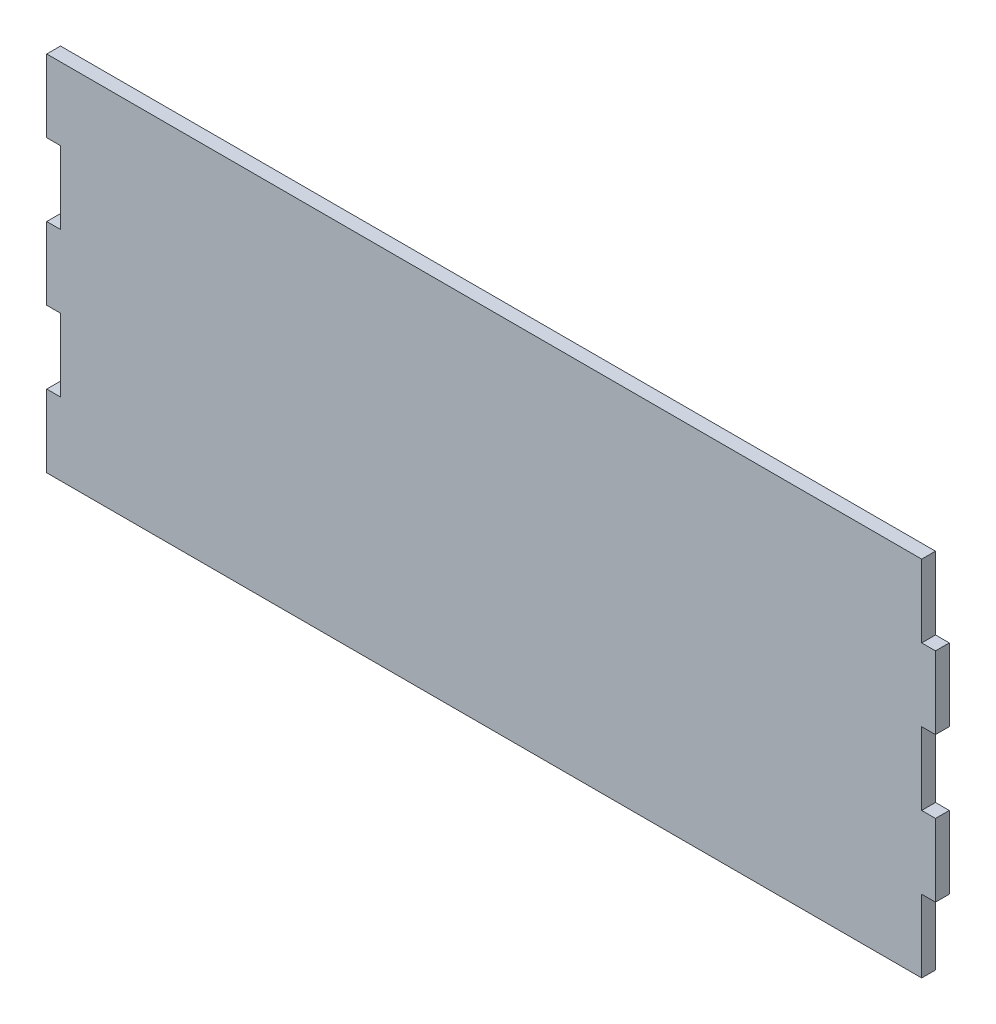
SolidWorks part; units mm, degrees
material "1060 Alloy"
ref_plane "Front Plane" through (0, 0, 0) normal (0, 0, 1) x (1, 0, 0)
ref_plane "Top Plane" through (0, 0, 0) normal (0, 1, 0) x (1, 0, 0)
ref_plane "Right Plane" through (0, 0, 0) normal (1, 0, 0) x (0, 0, -1)
sketch "Sketch1" plane through (0, 0, 0) normal (0, 0, 1) x (1, 0, 0)
  line L0 (-306.324, 101.6) -> (-306.324, 127)
  line L1 (0, 0) -> (-306.324, 0)
  line L2 (0, 0) -> (0, 25.4)
  line L3 (0, 127) -> (-306.324, 127)
  line L4 (-306.324, 0) -> (-306.324, 25.4)
  line L5 (0, 101.6) -> (4.826, 101.6)
  line L7 (0, 76.2) -> (4.826, 76.2)
  line L8 (4.826, 101.6) -> (4.826, 76.2)
  line L9 (0, 50.8) -> (4.826, 50.8)
  line L11 (0, 25.4) -> (4.826, 25.4)
  line L12 (4.826, 50.8) -> (4.826, 25.4)
  line L13 (-306.324, 50.8) -> (-301.498, 50.8)
  line L14 (0, 50.8) -> (0, 76.2)
  line L15 (-306.324, 25.4) -> (-301.498, 25.4)
  line L16 (-301.498, 50.8) -> (-301.498, 25.4)
  line L17 (-306.324, 101.6) -> (-301.498, 101.6)
  line L18 (0, 101.6) -> (0, 127)
  line L19 (-306.324, 76.2) -> (-301.498, 76.2)
  line L20 (-301.498, 101.6) -> (-301.498, 76.2)
  line L21 (-306.324, 50.8) -> (-306.324, 76.2)
  dimension "D1" = 127
  dimension "D2" = 4.826
  dimension "D3" = 311.15
extrude "Boss-Extrude1" add sketch "Sketch1" along normal blind 4.826 contours L3 L0 L17 L20 L19 L21 L13 L16 L15 L4 L1 L2 L11 L12 L9 L14 L7 L8 L5 L18
equation "\"w\"= .19"
equation "\"D2@Sketch1\"=\"w\""
equation "\"D1@Boss-Extrude1\"=\"w\""
